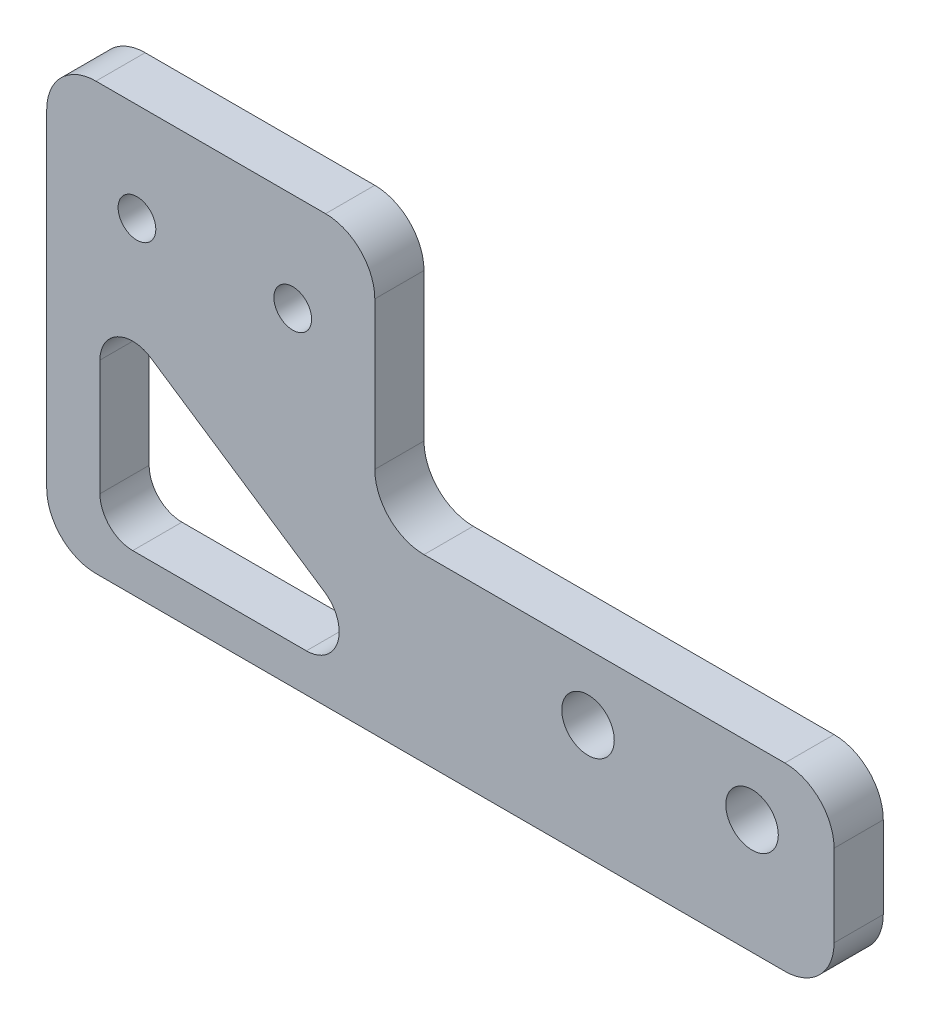
SolidWorks part; units mm, degrees
material "A-玻璃纤维"
ref_plane "前视基准面" through (0, 0, 0) normal (0, 0, 1) x (1, 0, 0)
ref_plane "上视基准面" through (0, 0, 0) normal (0, 1, 0) x (1, 0, 0)
ref_plane "右视基准面" through (0, 0, 0) normal (1, 0, 0) x (0, 0, -1)
sketch "草图1" plane through (0, 0, 0) normal (0, 0, 1) x (1, 0, 0)
  line L0 (0, 47.1437) -> (0, -40.3714) construction
  line L1 (73.0018, 0) -> (-78.485, 0) construction
  line L2 (5.5, 62.5) -> (5.5, 15) construction
  line L3 (0, 0) -> (48, 0)
  line L4 (0, 0) -> (0, 67.5)
  line L5 (0, 67.5) -> (48, 67.5)
  line L6 (48, 0) -> (48, 67.5)
  line L9 (6.65, 62.5) -> (6.65, 15) construction
  line L10 (4.35, 62.5) -> (4.35, 15) construction
  line L11 (15, 62.5) -> (15, 15) construction
  line L12 (16.15, 62.5) -> (16.15, 15) construction
  line L13 (13.85, 62.5) -> (13.85, 15) construction
  circle A0 centre (33, 7) radius 1.6
  circle A1 centre (43, 7) radius 1.6
  arc A4 (6.65, 62.5) -> (4.35, 62.5) centre (5.5, 62.5) ccw construction
  arc A5 (4.35, 15) -> (6.65, 15) centre (5.5, 15) ccw construction
  arc A6 (16.15, 62.5) -> (13.85, 62.5) centre (15, 62.5) ccw construction
  arc A7 (13.85, 15) -> (16.15, 15) centre (15, 15) ccw construction
  circle A8 centre (5.5, 20) radius 1.15
  circle A9 centre (15, 20) radius 1.15
  point P15 (5.5, 38.75)
  point P22 (15, 38.75)
  dimension "D1" = 10
  dimension "D2" = 3.2
  dimension "D3" = 5
  dimension "D6" = 15
  dimension "D8" = 2.3
  dimension "D9" = 48
  dimension "D10" = 9.5
  dimension "D12" = 18
  dimension "D13" = 2.3
  dimension "D14" = 9.5
  dimension "D15" = 13
  dimension "D4" = 47.5
  dimension "D5" = 18
  dimension "D7" = 7
  dimension "D11" = 5
extrude "凸台-拉伸1" add sketch "草图1" along normal blind 3
sketch "草图3" plane through (0, 0, 3) normal (0, 0, 1) x (1, 0, 0)
  line L0 (48, 11) -> (20, 11)
  line L1 (48, 0) -> (48, 67.5) construction
  line L2 (20, 11) -> (20, 67.5)
  line L3 (48, 67.5) -> (0, 67.5) construction
  line L4 (20, 67.5) -> (48, 67.5)
  line L5 (48, 67.5) -> (48, 11)
  circle A0 centre (43, 7) radius 1.6 construction
  dimension "D1" = 4
  dimension "D2" = 28
extrude "切除-拉伸1" cut sketch "草图3" against normal through all
fillet "圆角1" radius 3 6 edges at (20, 67.5, 1.5) (0, 67.5, 1.5) (0, 0, 1.5) (48, 0, 1.5) (48, 11, 1.5) (20, 11, 1.5)
sketch "草图5" plane through (0, 0, 3) normal (0, 0, 1) x (1, 0, 0)
  line L1 (-5.7467, 69.8403) -> (31.6167, 69.8403)
  line L2 (-5.7467, 69.8403) -> (-5.7467, 26)
  line L3 (-5.7467, 26) -> (31.6167, 26)
  line L4 (31.6167, 69.8403) -> (31.6167, 26)
  circle A0 centre (15, 20) radius 1.15 construction
  dimension "D1" = 6
extrude "切除-拉伸2" cut sketch "草图5" against normal blind 10
fillet "圆角2" radius 3 2 edges at (20, 26, 1.5) (0, 26, 1.5)
sketch "草图6" plane through (0, 0, 3) normal (0, 0, 1) x (1, 0, 0)
  line L0 (3.2432, 15.1276) -> (3.2432, 2.3348)
  line L1 (3.2432, 2.3348) -> (22.4354, 2.3348)
  line L2 (22.4354, 2.3348) -> (3.2432, 15.1276)
extrude "切除-拉伸3" cut sketch "草图6" against normal blind 10
fillet "圆角3" radius 2 3 edges at (22.4354, 2.3348, 1.5) (3.2432, 2.3348, 1.5) (3.2432, 15.1276, 1.5)
